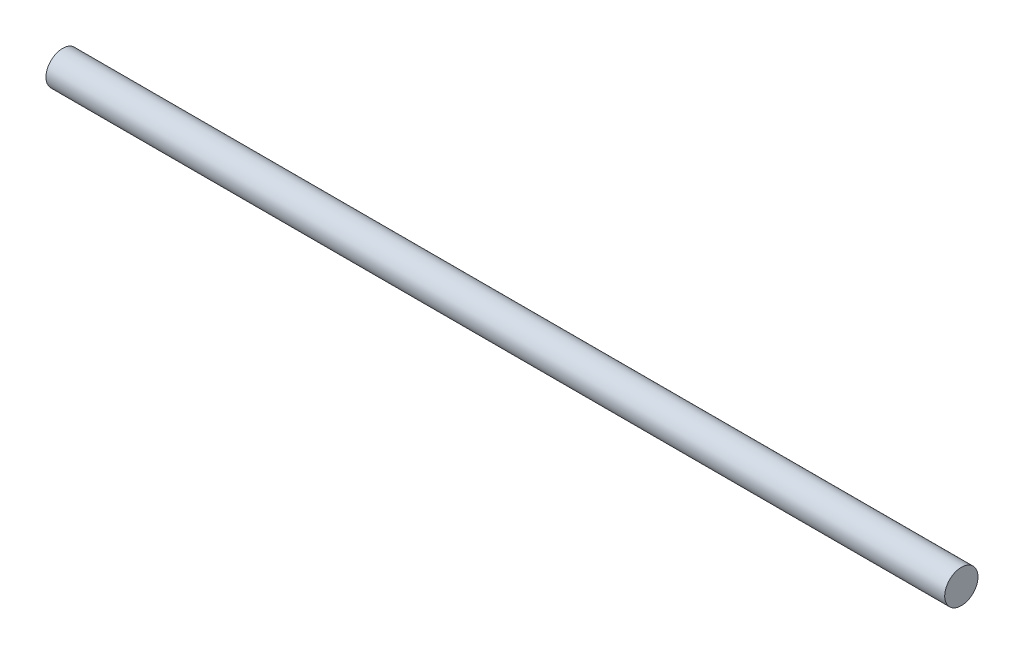
SolidWorks part; units mm, degrees
ref_plane "Front Plane" through (0, 0, 0) normal (0, 0, 1) x (1, 0, 0)
ref_plane "Top Plane" through (0, 0, 0) normal (0, 1, 0) x (1, 0, 0)
ref_plane "Right Plane" through (0, 0, 0) normal (1, 0, 0) x (0, 0, -1)
sketch "Sketch1" plane through (0, 0, 0) normal (1, 0, 0) x (0, 0, -1)
  circle A0 centre (0, 0) radius 6.35
  dimension "D1" = 12.7
extrude "Boss-Extrude1" add sketch "Sketch1" along normal mid plane 342.9
